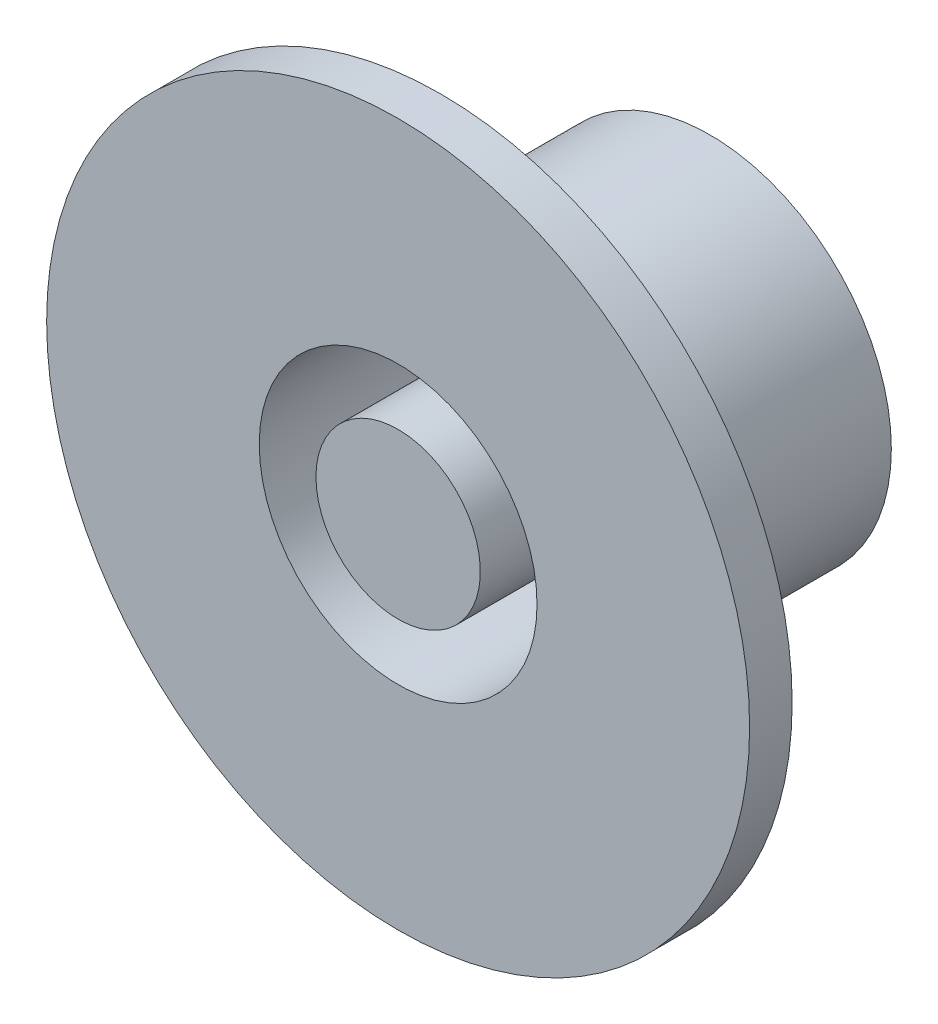
SolidWorks part; units mm, degrees
material "Alumina"
ref_plane "Front Plane" through (0, 0, 0) normal (0, 0, 1) x (1, 0, 0)
ref_plane "Top Plane" through (0, 0, 0) normal (0, 1, 0) x (1, 0, 0)
ref_plane "Right Plane" through (0, 0, 0) normal (1, 0, 0) x (0, 0, -1)
sketch "Sketch2" plane through (0, 0, 0) normal (1, 0, 0) x (0, 0, -1)
  line L0 (-22, 0) -> (-22, 5.8)
  line L1 (-22, 5.8) -> (-3, 5.8)
  line L2 (0, 4) -> (0, 12.8)
  line L3 (-3, 5.8) -> (-3, 9.8)
  line L7 (0, 4) -> (-19, 4)
  line L8 (-19, 4) -> (-19, 0)
  line L9 (-19, 0) -> (-22, 0)
  line L10 (0, 0) -> (-31.5977, 0) construction
  line L11 (0, -12.5) -> (0, 12.5) construction
  line L12 (-3, 9.8) -> (-22, 9.8)
  line L14 (0, 12.8) -> (-19, 12.8)
  line L16 (-22, 9.8) -> (-22, 24.8)
  line L18 (-19, 12.8) -> (-19, 24.8)
  line L19 (-19, 24.8) -> (-22, 24.8)
  dimension "D1" = 5.8
  dimension "D4" = 19
  dimension "D6" = 3
  dimension "D2" = 3
  dimension "D3" = 4
  dimension "D5" = 9.8
  dimension "D7" = 0
  dimension "D8" = 3
  dimension "D9" = 19
  dimension "D10" = 3
  dimension "D11" = 15
revolve "Revolve1" add sketch "Sketch2" angle 360 about L10
sketch "Sketch4" plane through (0, 0, 3) normal (0, 0, 1) x (1, 0, 0)
  line L0 (0, 0) -> (0, 20.7363) construction
  circle A0 centre (0, 0) radius 7.5 construction
  circle A8 centre (0, 7.5) radius 1.05
  circle A9 centre (5.3033, 5.3033) radius 1.05
  circle A10 centre (7.5, 0) radius 1.05
  circle A11 centre (5.3033, -5.3033) radius 1.05
  circle A12 centre (0, -7.5) radius 1.05
  circle A13 centre (-5.3033, -5.3033) radius 1.05
  circle A14 centre (-7.5, 0) radius 1.05
  circle A15 centre (-5.3033, 5.3033) radius 1.05
  point P21 (-0.5192, -1.0661)
  point P23 (0, 0)
  dimension "D1" = 15
  dimension "D2" = 8
extrude "Cut-Extrude1" cut sketch "Sketch4" against normal through all
equation "\"D9@Sketch2\"=\"D4@Sketch2\""
equation "\"D10@Sketch2\"=\"D6@Sketch2\""
